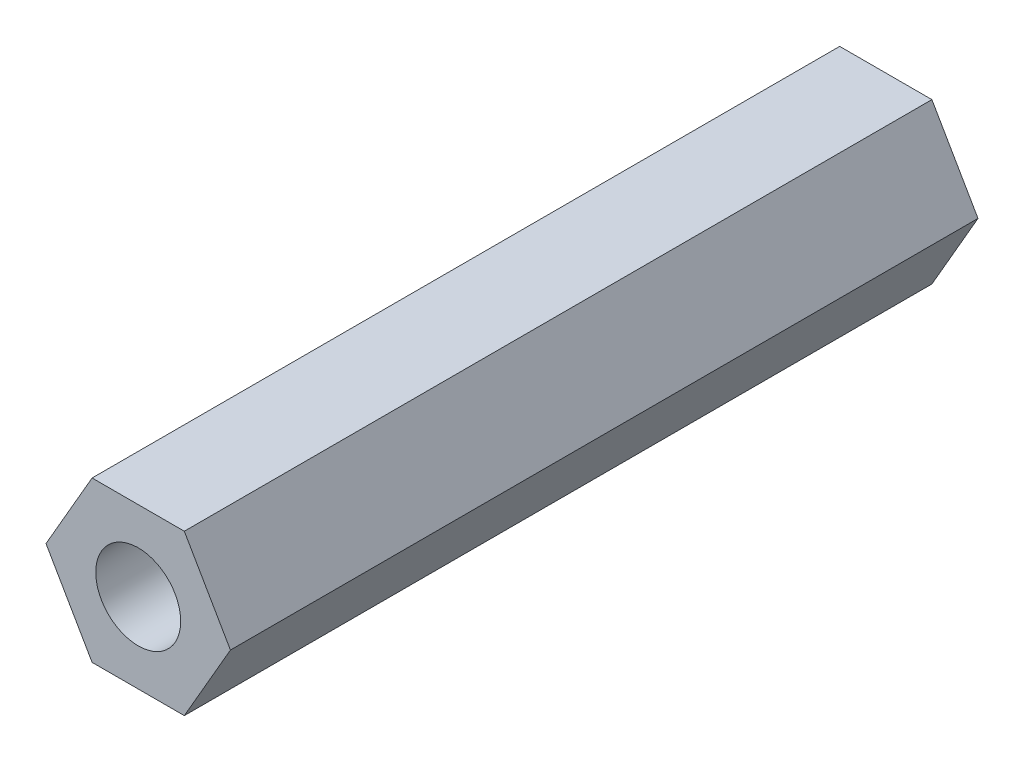
SolidWorks part; units mm, degrees
material "6061 合金"
ref_plane "前视基准面" through (0, 0, 0) normal (0, 0, 1) x (1, 0, 0)
ref_plane "上视基准面" through (0, 0, 0) normal (0, 1, 0) x (1, 0, 0)
ref_plane "右视基准面" through (0, 0, 0) normal (1, 0, 0) x (0, 0, -1)
sketch "草图1" plane through (0, 0, 0) normal (0, 0, 1) x (1, 0, 0)
  line L1 (1.3568, 2.35) -> (-1.3568, 2.35)
  line L2 (-1.3568, 2.35) -> (-2.7135, 0)
  line L3 (-2.7135, 0) -> (-1.3568, -2.35)
  line L4 (-1.3568, -2.35) -> (1.3568, -2.35)
  line L5 (1.3568, -2.35) -> (2.7135, 0)
  line L6 (2.7135, 0) -> (1.3568, 2.35)
  circle A0 centre (0, 0) radius 2.35 construction
  dimension "D1" = 4.7
extrude "凸台-拉伸1" add sketch "草图1" along normal mid plane 22
hole_wizard "M3 螺纹孔1" positions "草图2" profile "草图3" tap size "M3" standard "GB" end condition through all
sketch "草图2" plane through (0, 0, 11) normal (0, 0, 1) x (1, 0, 0)
  point P0 (0, 0)
sketch "草图3" plane through (0, 0, 11) normal (1, 0, 0) x (0, -1, 0)
  line L0 (0, 0) -> (0, 22)
  line L1 (0, 22) -> (1.25, 22)
  line L2 (1.25, 22) -> (1.25, 0)
  line L5 (1.25, 0) -> (0, 0)
  line L11 (0, -6.35) -> (0, 107.95) construction
  dimension "通孔螺纹孔钻头直径" = 2.5
  dimension "通孔螺纹孔钻头深度" = 22
cosmetic thread "孔螺蚊线1" parameters "D2"=3
